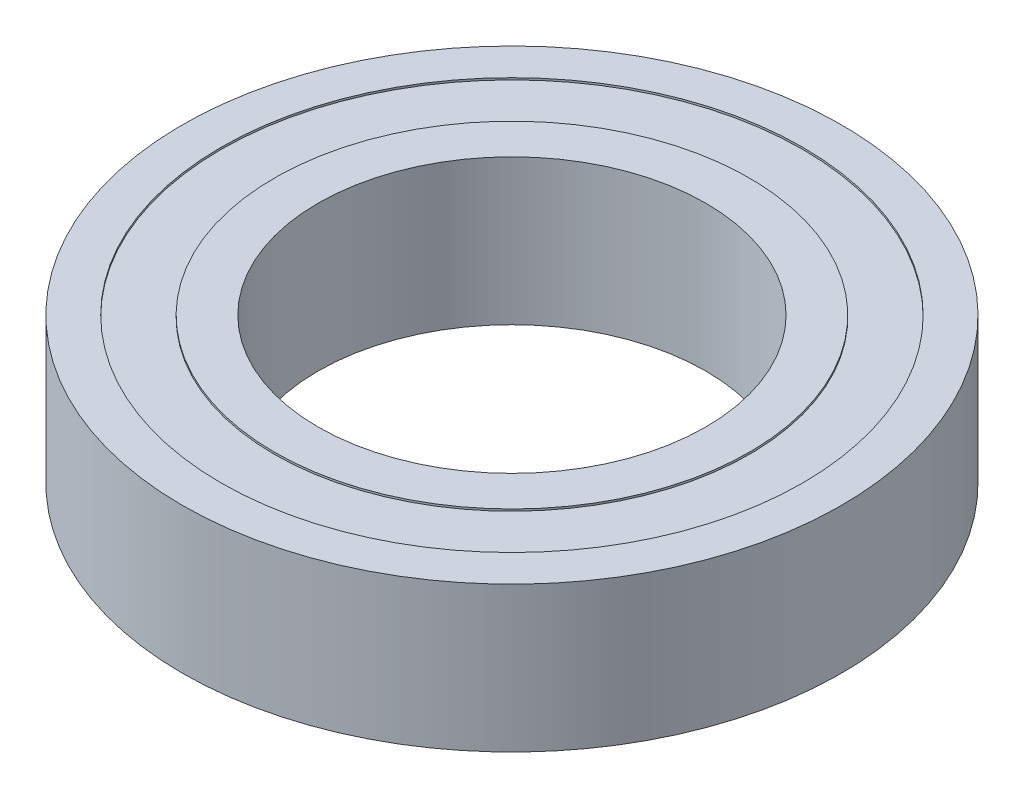
SolidWorks part; units mm, degrees
material "1023 Tôle d'acier au carbone (SS)"
ref_plane "Plan de face" through (0, 0, 0) normal (0, 0, 1) x (1, 0, 0)
ref_plane "Plan de dessus" through (0, 0, 0) normal (0, 1, 0) x (1, 0, 0)
ref_plane "Plan de droite" through (0, 0, 0) normal (1, 0, 0) x (0, 0, -1)
sketch "Esquisse1" plane through (0, 0, 0) normal (0, 1, 0) x (1, 0, 0)
  circle A0 centre (0, 0) radius 20
  circle A1 centre (0, 0) radius 34
  dimension "D1" = 40
  dimension "D2" = 68
extrude "Boss.-Extru.1" add sketch "Esquisse1" along normal blind 15
sketch "Esquisse2" plane through (0, 15, 0) normal (0, 1, 0) x (1, 0, 0)
  circle A0 centre (0, 0) radius 24.5
  circle A1 centre (0, 0) radius 30
  circle A2 centre (0, 0) radius 20 construction
  circle A3 centre (0, 0) radius 34 construction
  dimension "D1" = 4.5
  dimension "D2" = 4
extrude "Enlèv. mat.-Extru.1" cut sketch "Esquisse2" against normal blind 0.2
sketch "Esquisse3" plane through (0, 0, 0) normal (0, -1, 0) x (1, 0, 0)
  circle A1 centre (0, 0) radius 30
  circle A2 centre (0, 0) radius 30
  circle A3 centre (0, 0) radius 24.5
  circle A4 centre (0, 0) radius 24.5
  dimension "D1" = 0
  dimension "D2" = 0
extrude "Enlèv. mat.-Extru.2" cut sketch "Esquisse3" against normal blind 0.2
